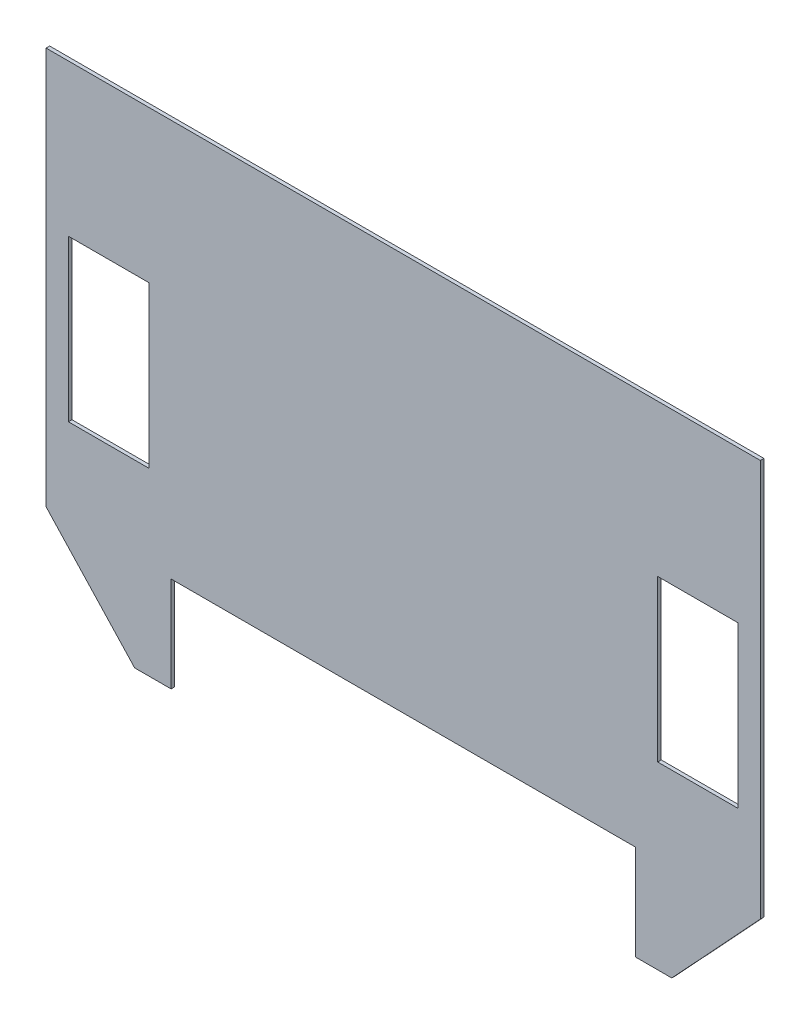
SolidWorks part; units mm, degrees
material "6061-T6 (SS)"
ref_plane "Front Plane" through (0, 0, 0) normal (0, 0, 1) x (1, 0, 0)
ref_plane "Top Plane" through (0, 0, 0) normal (0, 1, 0) x (1, 0, 0)
ref_plane "Right Plane" through (0, 0, 0) normal (1, 0, 0) x (0, 0, -1)
sketch "Sketch1" plane through (0, 0, 0) normal (0, 0, 1) x (1, 0, 0)
  line L0 (0, 0) -> (0, -179.6341) construction
  line L1 (200, 0) -> (-200, 0)
  line L2 (-200, 0) -> (-200, -222.5)
  line L3 (-200, -222.5) -> (-150.4043, -275.82)
  line L4 (-150.4043, -275.82) -> (-130, -275.82)
  line L5 (-130, -275.82) -> (-130, -222.5)
  line L6 (-130, -222.5) -> (130, -222.5)
  line L7 (130, -275.82) -> (130, -222.5)
  line L8 (150.4043, -275.82) -> (130, -275.82)
  line L9 (200, -222.5) -> (150.4043, -275.82)
  line L10 (200, 0) -> (200, -222.5)
  line L11 (187.5, -85) -> (142.5, -175) construction
  line L12 (-187.5, -85) -> (-142.5, -85)
  line L13 (-187.5, -85) -> (-187.5, -175)
  line L14 (-187.5, -175) -> (-142.5, -175)
  line L15 (-142.5, -85) -> (-142.5, -175)
  line L16 (-187.5, -85) -> (-142.5, -175) construction
  line L17 (-187.5, -175) -> (-142.5, -85) construction
  line L18 (187.5, -175) -> (142.5, -85) construction
  line L19 (187.5, -85) -> (187.5, -175)
  line L20 (187.5, -175) -> (142.5, -175)
  line L21 (142.5, -85) -> (142.5, -175)
  line L22 (187.5, -85) -> (142.5, -85)
  point P10 (0, -222.5)
  point P14 (-165, -130)
  dimension "D1" = 200
  dimension "D2" = 222.5
  dimension "D3" = 72.82
  dimension "D4" = 130
  dimension "D6" = 222.5
  dimension "D7" = 90
  dimension "D8" = 45
  dimension "D9" = 12.5
  dimension "D10" = 130
  dimension "D11" = 53.32
extrude "Boss-Extrude1" add sketch "Sketch1" along normal blind 2
